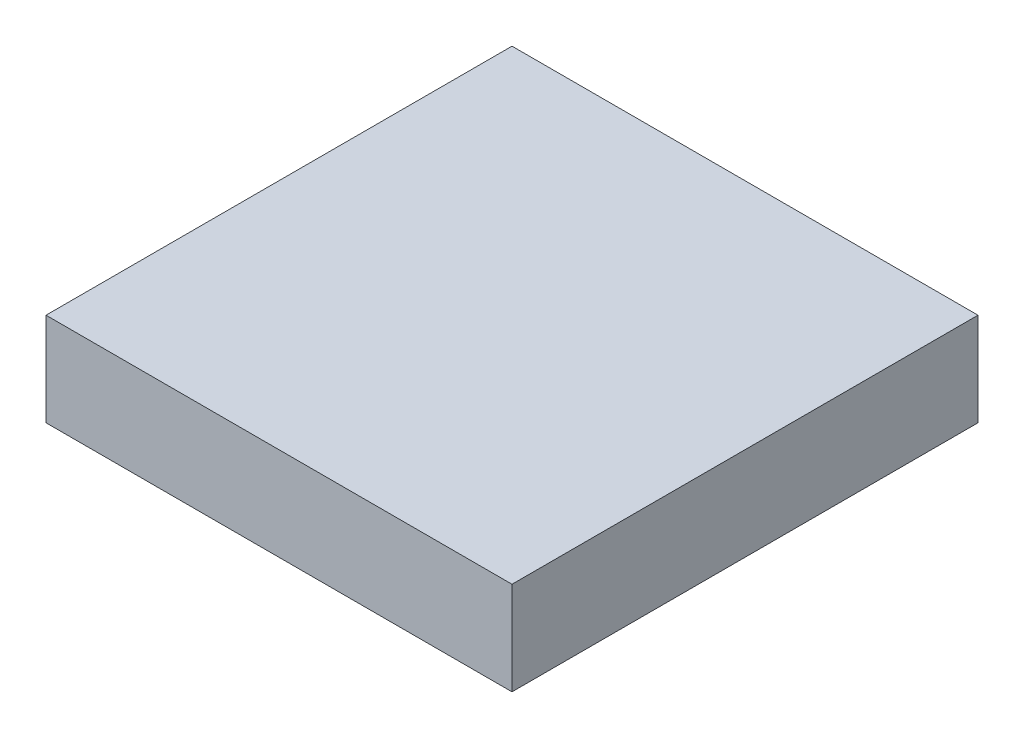
SolidWorks part; units mm, degrees
ref_plane "Front Plane" through (0, 0, 0) normal (0, 0, 1) x (1, 0, 0)
ref_plane "Top Plane" through (0, 0, 0) normal (0, 1, 0) x (1, 0, 0)
ref_plane "Right Plane" through (0, 0, 0) normal (1, 0, 0) x (0, 0, -1)
sketch "Sketch1" plane through (0, 0, 0) normal (0, 1, 0) x (1, 0, 0)
  line L1 (-7.5, -7.5) -> (7.5, -7.5)
  line L2 (-7.5, -7.5) -> (-7.5, 7.5)
  line L3 (-7.5, 7.5) -> (7.5, 7.5)
  line L4 (7.5, -7.5) -> (7.5, 7.5)
  line L5 (-7.5, -7.5) -> (7.5, 7.5) construction
  line L6 (-7.5, 7.5) -> (7.5, -7.5) construction
  point P0 (0, 0)
  dimension "D1" = 15
  dimension "D2" = 15
extrude "Boss-Extrude1" add sketch "Sketch1" along normal blind 3
sketch "Sketch2" plane through (0, 0, 0) normal (0, -1, 0) x (1, 0, 0)
  line L1 (-6, -6) -> (6, -6)
  line L2 (-6, -6) -> (-6, 6)
  line L3 (-6, 6) -> (6, 6)
  line L4 (6, -6) -> (6, 6)
  line L5 (-6, -6) -> (6, 6) construction
  line L6 (-6, 6) -> (6, -6) construction
  circle A0 centre (0, 0) radius 2.5
  point P0 (0, 0)
  dimension "D1" = 5
  dimension "D2" = 12
  dimension "D3" = 12
extrude "Cut-Extrude1" cut sketch "Sketch2" against normal blind 1.5
sketch "Sketch3" plane through (0, 0, 0) normal (0, -1, 0) x (1, 0, 0)
  line L0 (7.5, -7.5) -> (-7.5, -7.5) construction
  line L1 (-7.5, -7.5) -> (-7.5, 7.5) construction
  line L2 (7.5, 7.5) -> (7.5, -7.5) construction
  line L3 (-7.5, 7.5) -> (7.5, 7.5) construction
  circle A0 centre (-6.7, 6.7) radius 0.75
  circle A1 centre (6.7, 6.7) radius 0.75
  circle A2 centre (6.7, -6.7) radius 0.75
  circle A3 centre (-6.7, -6.7) radius 0.75
  dimension "D1" = 1.5
  dimension "D2" = 1.5
  dimension "D3" = 1.5
  dimension "D4" = 1.5
  dimension "D11" = 0.8
  dimension "D5" = 0.8
  dimension "D6" = 0.8
  dimension "D7" = 0.8
  dimension "D8" = 0.8
  dimension "D9" = 0.8
  dimension "D10" = 0.8
  dimension "D12" = 0.8
extrude "Cut-Extrude2" cut sketch "Sketch3" against normal blind 2
